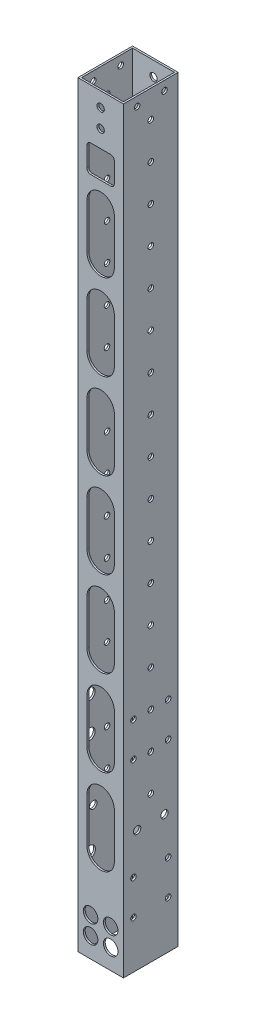
SolidWorks part; units mm, degrees
material "6063-T5"
ref_plane "前视基准面" through (0, 0, 0) normal (0, 0, 1) x (1, 0, 0)
ref_plane "上视基准面" through (0, 0, 0) normal (0, 1, 0) x (1, 0, 0)
ref_plane "右视基准面" through (0, 0, 0) normal (1, 0, 0) x (0, 0, -1)
other "Configuration Table"
sketch "草图2" plane through (0, 0, 0) normal (0, 1, 0) x (1, 0, 0)
  line L1 (-12.5, -15) -> (12.5, -15)
  line L2 (-12.5, -15) -> (-12.5, 15)
  line L3 (-12.5, 15) -> (12.5, 15)
  line L4 (12.5, -15) -> (12.5, 15)
  line L5 (-12.5, -15) -> (12.5, 15) construction
  line L6 (-12.5, 15) -> (12.5, -15) construction
  point P0 (0, 0)
  dimension "D1" = 25
  dimension "D2" = 30
extrude "凸台-拉伸1" add sketch "草图2" along normal mid plane 415
sketch "草图3" plane through (0, 0, 0) normal (0, 1, 0) x (1, 0, 0)
  line L8 (11.5, -14) -> (11.5, 14)
  line L9 (11.5, 14) -> (-11.5, 14)
  line L10 (-11.5, 14) -> (-11.5, -14)
  line L11 (-11.5, -14) -> (11.5, -14)
  line L12 (11.5, -14) -> (11.5, 14)
  line L13 (11.5, 14) -> (-11.5, 14)
  line L14 (-11.5, 14) -> (-11.5, -14)
  line L15 (-11.5, -14) -> (11.5, -14)
  dimension "D1" = 1
extrude "切除-拉伸1" cut sketch "草图3" against normal through all both and the other way through all
sketch "草图4" plane through (-12.5, 0, 0) normal (-1, 0, 0) x (0, 0, 1)
  line L0 (-15, -207.5) -> (15, -207.5) construction
  line L1 (-9.5, -181.5) -> (9.5, -181.5) construction
  line L2 (-9.5, -181.5) -> (-9.5, -162.5) construction
  line L3 (-9.5, -162.5) -> (9.5, -162.5) construction
  line L4 (9.5, -181.5) -> (9.5, -162.5) construction
  line L5 (-9.5, -181.5) -> (9.5, -162.5) construction
  line L6 (-9.5, -162.5) -> (9.5, -181.5) construction
  circle A0 centre (-9.5, -162.5) radius 1.525
  circle A1 centre (9.5, -162.5) radius 1.525
  circle A2 centre (9.5, -181.5) radius 1.525
  circle A3 centre (-9.5, -181.5) radius 1.525
  point P0 (0, -172)
  point P7 (0, -207.5)
  dimension "D3" = 3.05
  dimension "D1" = 19
  dimension "D2" = 26
extrude "切除-拉伸2" cut sketch "草图4" against normal through all both and the other way through all
sketch "草图5" plane through (-12.5, 0, 0) normal (-1, 0, 0) x (0, 0, 1)
  circle A4 centre (-9.5, -162.5) radius 3.15
  circle A5 centre (-9.5, -181.5) radius 3.15
  circle A6 centre (9.5, -162.5) radius 3.15
  circle A7 centre (9.5, -181.5) radius 3.15
  dimension "D1" = 6.3
extrude "切除-拉伸3" cut sketch "草图5" against normal up to next
sketch "草图6" plane through (0, 0, -15) normal (0, 0, -1) x (-1, 0, 0)
  line L0 (-12.5, 207.5) -> (12.5, 207.5) construction
  line L1 (-5, 189.5) -> (5, 189.5) construction
  line L2 (-5, 189.5) -> (-5, 199.5) construction
  line L3 (-5, 199.5) -> (5, 199.5) construction
  line L4 (5, 189.5) -> (5, 199.5) construction
  line L5 (-5, 189.5) -> (5, 199.5) construction
  line L6 (-5, 199.5) -> (5, 189.5) construction
  circle A4 centre (0, 199.5) radius 2.025
  circle A5 centre (0, 189.5) radius 2.025
  point P0 (0, 194.5)
  dimension "D3" = 4.05
  dimension "D1" = 10
  dimension "D2" = 10
  dimension "D4" = 8
extrude "切除-拉伸4" cut sketch "草图6" against normal through all
sketch "草图7" plane through (0, 0, 15) normal (0, 0, 1) x (1, 0, 0)
  line L0 (-12.5, -207.5) -> (12.5, -207.5) construction
  line L1 (-5.5, -196.5) -> (5.5, -196.5) construction
  line L2 (-5.5, -196.5) -> (-5.5, -186.5) construction
  line L3 (-5.5, -186.5) -> (5.5, -186.5) construction
  line L4 (5.5, -196.5) -> (5.5, -186.5) construction
  line L5 (-5.5, -196.5) -> (5.5, -186.5) construction
  line L6 (-5.5, -186.5) -> (5.5, -196.5) construction
  circle A0 centre (-5.5, -186.5) radius 2.025
  circle A1 centre (-5.5, -196.5) radius 2.025
  circle A2 centre (5.5, -196.5) radius 2.025
  circle A3 centre (5.5, -186.5) radius 2.025
  point P0 (0, -191.5)
  dimension "D4" = 4.05
  dimension "D1" = 10
  dimension "D2" = 11
  dimension "D3" = 11
extrude "切除-拉伸5" cut sketch "草图7" against normal through all both and the other way through all
sketch "草图8" plane through (0, 0, 15) normal (0, 0, 1) x (1, 0, 0)
  circle A0 centre (-5.5, -186.5) radius 4
  circle A1 centre (5.5, -186.5) radius 4
  circle A2 centre (5.5, -196.5) radius 4
  circle A3 centre (-5.5, -196.5) radius 4
  dimension "D1" = 8
extrude "切除-拉伸6" cut sketch "草图8" against normal blind 10
sketch "草图9" plane through (-12.5, 0, 0) normal (-1, 0, 0) x (0, 0, 1)
  circle A0 centre (9.5, -106.5) radius 1.525
  circle A1 centre (-9.5, -106.5) radius 1.525
  circle A2 centre (9.5, -87.5) radius 1.525
  circle A3 centre (-9.5, -87.5) radius 1.525
  circle A4 centre (9.5, -87.5) radius 1.5 construction
  circle A5 centre (9.5, -106.5) radius 1.2 construction
  circle A7 centre (-9.5, -87.5) radius 1.2 construction
  circle A8 centre (-9.5, -106.5) radius 1.5 construction
  dimension "D1" = 3.05
extrude "切除-拉伸7" cut sketch "草图9" against normal through all both
sketch "草图10" plane through (-12.5, 0, 0) normal (-1, 0, 0) x (0, 0, 1)
  circle A0 centre (9.5, -87.5) radius 3
  circle A1 centre (9.5, -106.5) radius 3
  circle A2 centre (-9.5, -87.5) radius 3
  circle A3 centre (-9.5, -106.5) radius 3
  dimension "D1" = 6
  dimension "D2" = 6
extrude "切除-拉伸8" cut sketch "草图10" against normal blind 5
sketch "草图11" plane through (-12.5, 0, 0) normal (-1, 0, 0) x (0, 0, 1)
  circle A0 centre (0, -127.5) radius 1.525
  dimension "D1" = 3.05
extrude "切除-拉伸9" cut sketch "草图11" against normal through all
pattern_linear "阵列(线性)1" count 17 spacing 20 along (0, 1, 0) of "切除-拉伸9"
sketch "草图13" plane through (-12.5, 0, 0) normal (-1, 0, 0) x (0, 0, 1)
  circle A0 centre (7.5, 202.5) radius 1.525
  circle A1 centre (-7.5, 202.5) radius 1.525
  dimension "D1" = 3.05
extrude "切除-拉伸10" cut sketch "草图13" against normal through all
sketch "草图14" plane through (-12.5, 0, 0) normal (-1, 0, 0) x (0, 0, 1)
  circle A0 centre (7.5, -141) radius 2.025
  circle A1 centre (-7.5, -141) radius 2.025
  dimension "D1" = 4.05
extrude "切除-拉伸11" cut sketch "草图14" against normal through all both
sketch "草图15" plane through (0, 0, 15) normal (0, 0, 1) x (1, 0, 0)
  line L0 (0, -155) -> (0, -130) construction
  line L1 (-7.5, -155) -> (-7.5, -130)
  line L2 (7.5, -155) -> (7.5, -130)
  line L3 (-12.5, -207.5) -> (12.5, -207.5) construction
  arc A0 (-7.5, -155) -> (7.5, -155) centre (0, -155) ccw
  arc A1 (7.5, -130) -> (-7.5, -130) centre (0, -130) ccw
  point P3 (0, -142.5)
  point P8 (-7.5, -142.5)
  dimension "D1" = 25
  dimension "D2" = 65
  dimension "D3" = 15
extrude "切除-拉伸12" cut sketch "草图15" against normal blind 5
pattern_linear "阵列(线性)2" count 7 spacing 47 along (0, 1, 0) of "切除-拉伸12"
sketch "草图17" plane through (0, 0, 15) normal (0, 0, 1) x (1, 0, 0)
  line L1 (-5.5, 165) -> (5.5, 165)
  line L2 (-7.5, 167) -> (-7.5, 178)
  line L3 (-5.5, 180) -> (5.5, 180)
  line L4 (7.5, 167) -> (7.5, 178)
  line L5 (-7.5, 165) -> (7.5, 180) construction
  line L6 (-7.5, 180) -> (7.5, 165) construction
  arc A0 (7.5, 152) -> (-7.5, 152) centre (0, 152) ccw construction
  arc A1 (-5.5, 165) -> (-7.5, 167) centre (-5.5, 167) cw
  arc A2 (5.5, 165) -> (7.5, 167) centre (5.5, 167) ccw
  arc A3 (5.5, 180) -> (7.5, 178) centre (5.5, 178) cw
  arc A4 (-7.5, 178) -> (-5.5, 180) centre (-5.5, 178) cw
  point P0 (0, 172.5)
  dimension "D4" = 2
  dimension "D1" = 15
  dimension "D2" = 15
  dimension "D3" = 28
extrude "切除-拉伸13" cut sketch "草图17" against normal through all both
sketch "草图18" plane through (0, 0, -15) normal (0, 0, -1) x (-1, 0, 0)
  line L0 (-7.5, -155) -> (-7.5, -130) construction
  line L1 (7.5, -130) -> (7.5, -155) construction
  line L2 (-7.5, -155) -> (-7.5, -130)
  line L3 (7.5, -130) -> (7.5, -155)
  arc A0 (-7.5, -155) -> (7.5, -155) centre (0, -155) ccw construction
  arc A1 (7.5, -130) -> (-7.5, -130) centre (0, -130) ccw construction
  arc A2 (-7.5, -155) -> (7.5, -155) centre (0, -155) ccw
  arc A3 (7.5, -130) -> (-7.5, -130) centre (0, -130) ccw
extrude "切除-拉伸14" cut sketch "草图18" against normal through all both
sketch "草图19" plane through (0, 0, -15) normal (0, 0, -1) x (-1, 0, 0)
  line L0 (0, -33) -> (0, -23) construction
  line L1 (-7, -33) -> (-7, -23)
  line L2 (7, -33) -> (7, -23)
  line L3 (0, -62) -> (0, -72) construction
  line L4 (7, -62) -> (7, -72)
  line L5 (-7, -62) -> (-7, -72)
  line L6 (0, 68) -> (0, 78) construction
  line L7 (-7, 68) -> (-7, 78)
  line L8 (7, 68) -> (7, 78)
  line L9 (0, 108) -> (0, 118) construction
  line L10 (-7, 108) -> (-7, 118)
  line L11 (7, 108) -> (7, 118)
  arc A0 (-7, -33) -> (7, -33) centre (0, -33) ccw
  arc A1 (7, -23) -> (-7, -23) centre (0, -23) ccw
  arc A2 (7, -62) -> (-7, -62) centre (0, -62) ccw
  arc A3 (-7, -72) -> (7, -72) centre (0, -72) ccw
  arc A4 (-7, 68) -> (7, 68) centre (0, 68) ccw
  arc A5 (7, 78) -> (-7, 78) centre (0, 78) ccw
  arc A6 (-7, 108) -> (7, 108) centre (0, 108) ccw
  arc A7 (7, 118) -> (-7, 118) centre (0, 118) ccw
  point P3 (0, -28)
  point P10 (0, -67)
  point P17 (0, 73)
  point P22 (0, 113)
  point P29 (7, 73)
  dimension "D1" = 7
  dimension "D2" = 10
  dimension "D3" = 28
  dimension "D4" = 67
  dimension "D5" = 73
  dimension "D6" = 113
extrude "切除-拉伸15" cut sketch "草图19" against normal blind 10
sketch "草图20" plane through (12.5, 0, 0) normal (1, 0, 0) x (0, 0, -1)
  circle A0 centre (0, 152.5) radius 2.025
  circle A1 centre (0, 132.5) radius 2.025
  dimension "D1" = 4.05
